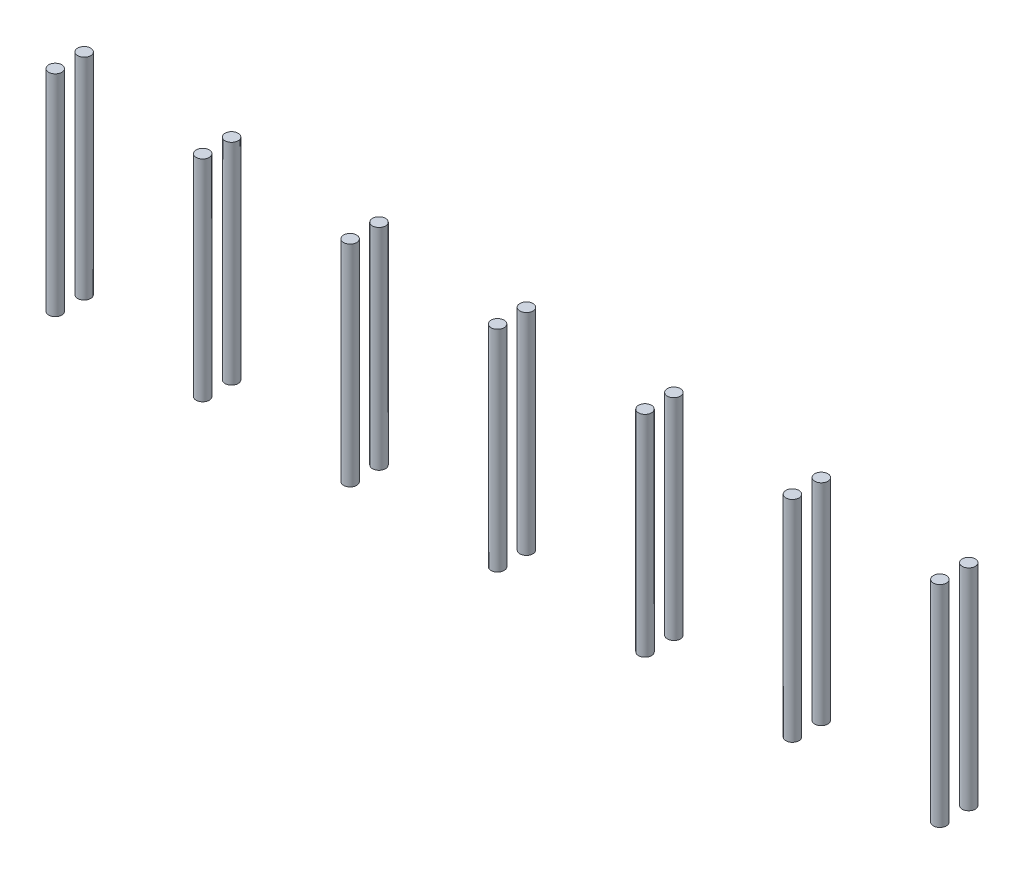
SolidWorks part; units mm, degrees
ref_plane "Front Plane" through (0, 0, 0) normal (0, 0, 1) x (1, 0, 0)
ref_plane "Top Plane" through (0, 0, 0) normal (0, 1, 0) x (1, 0, 0)
ref_plane "Right Plane" through (0, 0, 0) normal (1, 0, 0) x (0, 0, -1)
sketch "Sketch1" plane through (0, -1, 0) normal (0, 1, 0) x (1, 0, 0)
  circle A0 centre (-66.5, 42) radius 3.175
  circle A2 centre (-66.5, 42) radius 3.175 construction
  circle A3 centre (-66.5, 28) radius 3.175
  circle A4 centre (-66.5, 28) radius 3.175 construction
  circle A6 centre (5, 42) radius 3.175
  circle A7 centre (5, 28) radius 3.175
  circle A8 centre (76.5, 42) radius 3.175
  circle A9 centre (76.5, 28) radius 3.175
  circle A10 centre (148, 42) radius 3.175
  circle A11 centre (148, 28) radius 3.175
  circle A12 centre (219.5, 42) radius 3.175
  circle A13 centre (219.5, 28) radius 3.175
  circle A14 centre (291, 42) radius 3.175
  circle A15 centre (291, 28) radius 3.175
  circle A16 centre (362.5, 42) radius 3.175
  circle A17 centre (362.5, 28) radius 3.175
  dimension "D1" = 7
extrude "Boss-Extrude1" add sketch "Sketch1" along normal up to surface (102 mm away)
